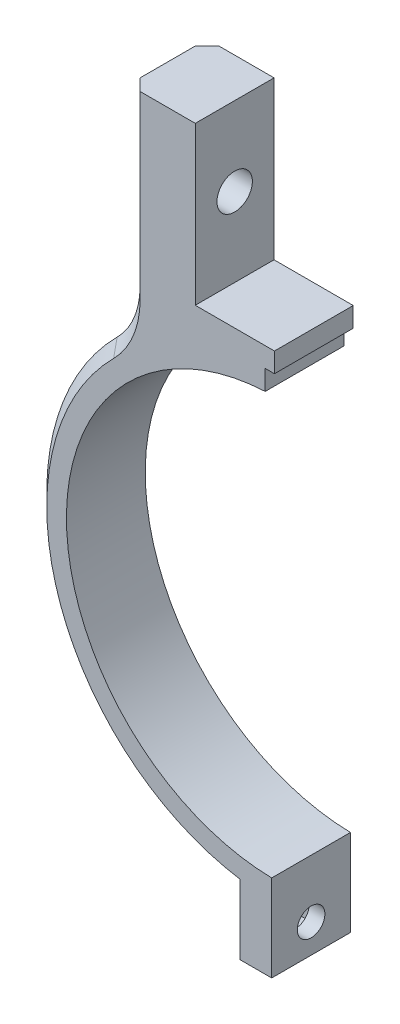
SolidWorks part; units mm, degrees
ref_plane "Ebene vorne" through (0, 0, 0) normal (0, 0, 1) x (1, 0, 0)
ref_plane "Ebene oben" through (0, 0, 0) normal (0, 1, 0) x (1, 0, 0)
ref_plane "Ebene rechts" through (0, 0, 0) normal (1, 0, 0) x (0, 0, -1)
sketch "Skizze1" plane through (0, 0, 0) normal (0, 0, 1) x (1, 0, 0)
  line L0 (0, 0) -> (0, 53.7291) construction
  line L14 (0, 0) -> (0, -44.1347) construction
  line L15 (0.5, -26.5453) -> (0.5, -30.5459)
  line L16 (-0.5, -26.5453) -> (-0.5, -30.5459)
  line L17 (0.5, -30.5459) -> (0.5, -37.5459)
  line L18 (0.5, -37.5459) -> (4.5, -37.5459)
  line L19 (4.5, -37.5459) -> (4.5, -30.2168)
  line L20 (-4.5, -37.5459) -> (-4.5, -30.2168)
  line L21 (-0.5, -37.5459) -> (-4.5, -37.5459)
  line L22 (-0.5, -30.5459) -> (-0.5, -37.5459)
  line L23 (-10.2, 31.55) -> (-10.2, 51.55)
  line L24 (-10.2, 51.55) -> (-18.7, 51.55)
  line L25 (-18.7, 51.55) -> (-18.7, 24.1581)
  line L26 (-10.2, 31.55) -> (10.2, 31.55)
  line L27 (0, 26.55) -> (12.0002, 26.55) construction
  line L28 (18.7, 51.55) -> (18.7, 24.1581)
  line L29 (10.2, 51.55) -> (18.7, 51.55)
  line L30 (10.2, 31.55) -> (10.2, 51.55)
  arc A0 (0.5, -26.5453) -> (-0.5, -26.5453) centre (0, 0) ccw
  arc A1 (-18.7, 24.1581) -> (-4.5, -30.2168) centre (0, 0) ccw
  arc A2 (4.5, -30.2168) -> (18.7, 24.1581) centre (0, 0) ccw
  point P10 (0, 33.5025)
  point P11 (0, 31.6594)
  point P17 (0, 31.55)
  point P18 (0, 39.6025)
  dimension "D1" = 53.1
  dimension "D2" = 4
  dimension "D3" = 20.4
  dimension "D4" = 20
  dimension "D5" = 5
  dimension "D6" = 8.5
  dimension "D10" = 1
  dimension "D11" = 4
  dimension "D12" = 7
extrude "Aufsatz-Linear austragen1" add sketch "Skizze1" along normal blind 10
sketch "Skizze2" plane through (-4.5, 0, 0) normal (-1, 0, 0) x (0, 0, 1)
  line L0 (0, -33.8813) -> (10, -33.8813) construction
  line L1 (0, -30.2168) -> (0, -37.5459) construction
  line L2 (10, -30.2168) -> (10, -37.5459) construction
  circle A0 centre (5, -33.8813) radius 1.75
  dimension "D1" = 3.5
extrude "Schnitt-Linear austragen1" cut sketch "Skizze2" against normal through all
sketch "Skizze3" plane through (0, 0, 10) normal (0, 0, 1) x (1, 0, 0)
  line L0 (-10.8174, 36.4205) -> (0, 26.8755)
  line L1 (0, 26.8755) -> (11.8484, 37.1414)
  line L2 (11.8484, 37.1414) -> (47.3746, 17.8863)
  line L3 (47.3746, 17.8863) -> (51.4546, -59.0738)
  line L4 (51.4546, -59.0738) -> (-81.1349, -43.2704)
  line L5 (-81.1349, -43.2704) -> (-40.9452, 68.8874)
  line L6 (-40.9452, 68.8874) -> (-10.8174, 36.4205)
extrude "Schnitt-Linear austragen2" [suppressed] cut sketch "Skizze3" against normal through all
sketch "Skizze4" plane through (-18.7, 0, 0) normal (-1, 0, 0) x (0, 0, 1)
  line L0 (5, 51.55) -> (5, 31.55) construction
  line L1 (10, 51.55) -> (0, 51.55) construction
  line L3 (10, 31.55) -> (0, 31.55) construction
  circle A0 centre (5, 41.55) radius 2.25
  dimension "D1" = 4.5
extrude "Schnitt-Linear austragen3" cut sketch "Skizze4" against normal through all
fillet "Verrundung1" radius 10 2 edges at (18.7, 24.1581, 5) (-18.7, 24.1581, 5)
sketch "Skizze5" plane through (-4.5, 0, 0) normal (-1, 0, 0) x (0, 0, 1)
  line L0 (5, -33.8813) -> (5, -27.6721) construction
  line L2 (2.225, -36.6563) -> (7.775, -36.6563)
  line L3 (2.225, -36.6563) -> (2.225, -31.1063)
  line L4 (2.225, -31.1063) -> (7.775, -31.1063)
  line L5 (7.775, -36.6563) -> (7.775, -31.1063)
  line L6 (2.225, -36.6563) -> (7.775, -31.1063) construction
  line L7 (2.225, -31.1063) -> (7.775, -36.6563) construction
  dimension "D1" = 5.55
extrude "Schnitt-Linear austragen4" cut sketch "Skizze5" against normal blind 2
sketch "Skizze6" plane through (0, 0, 0) normal (0, 0, 1) x (1, 0, 0)
  line L0 (0, 0) -> (0, 63.9135)
  line L1 (0, 63.9135) -> (40.0139, 63.9135)
  line L2 (40.0139, 63.9135) -> (48.3604, -54.8191)
  line L3 (48.3604, -54.8191) -> (0, -54.8191)
  line L4 (0, -54.8191) -> (0, 0)
extrude "Schnitt-Linear austragen5" cut sketch "Skizze6" along normal through all
chamfer "Fase1" distance 1.5 angle 45 6 edges at (-18.7, 40.0982, 0) (-19.4594, 24.8238, 0) (-29.0064, -9.5882, 0) (-18.7, 40.0982, 10) (-19.4594, 24.8238, 10) (-29.0064, -9.5882, 10)
sketch "Skizze7" plane through (0, 0, 10) normal (0, 0, 1) x (1, 0, 0)
  line L0 (0, 0) -> (0, 48.8265) construction
  line L1 (1.325, 29.05) -> (0, 29.05)
  line L2 (-1.325, 29.05) -> (-1.325, 23.5224)
  line L3 (-1.325, 23.5224) -> (1.325, 23.5224)
  line L4 (0, 26.55) -> (5.2959, 26.55) construction
  line L5 (1.325, 29.05) -> (1.325, 23.5224)
  line L6 (-0.15, 29.05) -> (-0.15, 31.55)
  line L7 (0, 31.55) -> (-10.2, 31.55) construction
  line L8 (-0.15, 31.55) -> (0, 31.55)
  line L9 (0, 31.55) -> (0, 29.05)
  line L10 (-0.15, 29.05) -> (-1.325, 29.05)
  point P11 (0, 23.5224)
  point P12 (0, 29.05)
  dimension "D1" = 2.5
  dimension "D2" = 2.65
  dimension "D3" = 0.15
extrude "Schnitt-Linear austragen6" cut sketch "Skizze7" against normal through all
